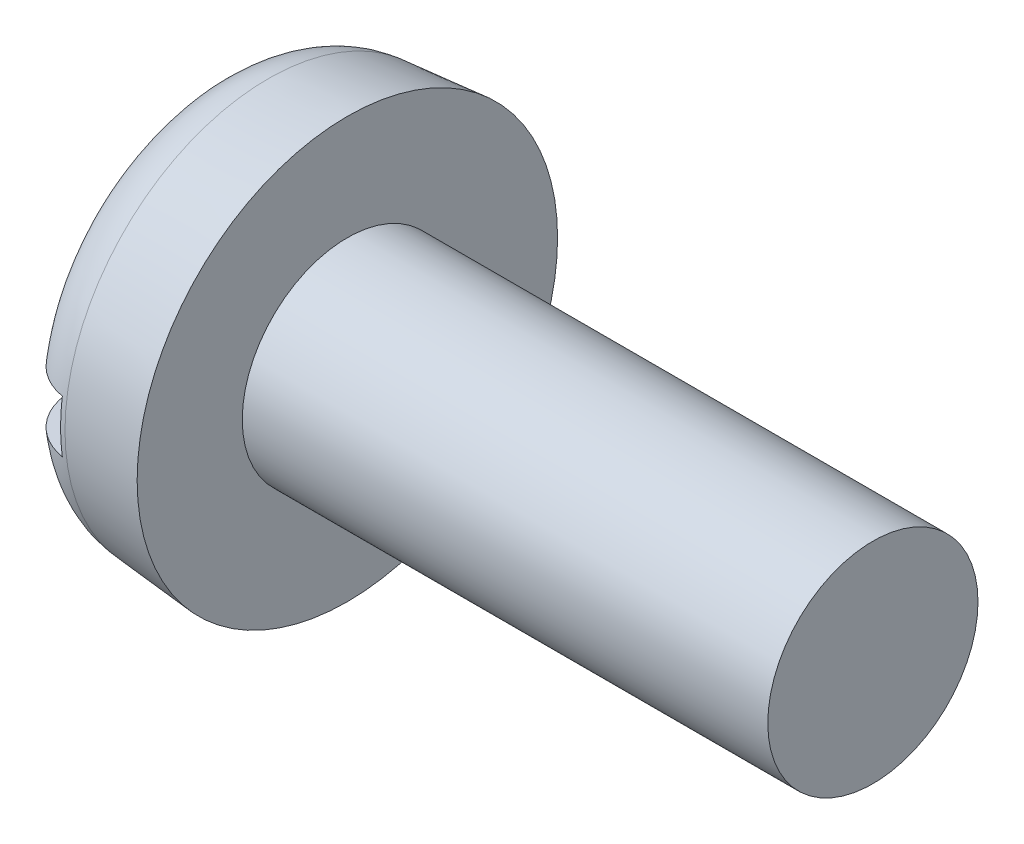
SolidWorks part; units mm, degrees
ref_plane "Plane1" through (0, 0, 0) normal (0, 0, 1) x (1, 0, 0)
ref_plane "Plane2" through (0, 0, 0) normal (0, 1, 0) x (1, 0, 0)
ref_plane "Plane3" through (0, 0, 0) normal (1, 0, 0) x (0, 0, -1)
sketch "BodySke" plane through (0, 0, 0) normal (0, 0, 1) x (1, 0, 0)
  line L0 (1.3, 1) -> (1.3, 2)
  line L1 (0, 0) -> (0, 1.8863)
  line L2 (-25.4, 0) -> (127, 0) construction
  line L3 (6.3, 0) -> (0, 0)
  line L4 (1.3, 1) -> (6.3, 1)
  line L5 (6.3, 1) -> (6.3, 0)
  line L6 (0, 1.8863) -> (1.3, 2)
  line L9 (1.7, 2.5875) -> (1.7, -6.9375) construction
  line L10 (1.3, 6.35) -> (1.3, -3.175) construction
  dimension "Head_ht" = 1.3
  dimension "Diameter" = 2
  dimension "Length" = 5
  dimension "Head_dia" = 4
  dimension "Advance" = 0.4
  dimension "Thread_nom" = 5
  dimension "Head_side_angle" = 5
revolve "Base-Revolve" add sketch "BodySke"
cosmetic thread "ThreadCosmetic"
fillet "Fillet1" [suppressed] radius 0.1
fillet "Fillet2" radius 0.6 1 edges at (0, 0, 1.8863)
sketch "Sketch2" plane through (0, 0, 0) normal (1, 0, 0) x (0, 0, -1)
  line L0 (2, -0.25) -> (-2, -0.25)
  line L1 (2, -0.25) -> (2, 0.25)
  line L2 (-2, 0.25) -> (2, 0.25)
  line L3 (-2, 0.25) -> (-2, -0.25)
  dimension "D1" = 4
  dimension "D2" = 2
  dimension "Slot_width" = 0.5
  dimension "D3" = 0.25
extrude "Slot" cut sketch "Sketch2" along normal blind 0.5
sketch "ThdSchSke" plane through (0, 0, 0) normal (0, 0, 1) x (1, 0, 0)
  line L0 (2.1, -0.774) -> (1.9418, -1)
  line L1 (2.1, -0.774) -> (2.2582, -1)
  line L2 (2.2582, -1) -> (2.2582, -1.25)
  line L3 (-3.175, 0) -> (5.1513, 0) construction
  line L5 (2.2582, -1.25) -> (1.9418, -1.25)
  line L6 (1.9418, -1.25) -> (1.9418, -1)
  dimension "Thread_minor" = 1.548
  dimension "Diameter" = 2
  dimension "Start" = 2.1
  dimension "SideAngle" = 55
  dimension "VeeAngle" = 70
  dimension "Overcut" = 2.5
revolve "ThreadSchematic" [suppressed] cut sketch "ThdSchSke" angle 360 about L3
pattern_linear "ThdSchPat" [suppressed]
equation "\"D1@Sketch2\" = \"Head_dia@BodySke\""
equation "\"D2@Sketch2\" = \"D1@Sketch2\" / 2"
equation "\"D3@Sketch2\" = \"Slot_width@Sketch2\" / 2"
equation "\"Thread_length@ThreadCosmetic\" = ((sgn( (\"Length@BodySke\" - \"Advance@BodySke\" * 2.0 ) - \"Thread_nom@BodySke\" )-1)*( (\"Length@BodySke\" - \"Advance@BodySke\"  * 2.0) - \"Thread_nom@BodySke\" ))/-2+ \"Thread_nom@BodySke\""
equation "\"Thread_minor@ThdSchSke\" = \"Thread_minor@ThreadCosmetic\""
equation "\"Diameter@ThdSchSke\" = \"Diameter@BodySke\""
equation "\"Overcut@ThdSchSke\" = \"Diameter@BodySke\" * 1.25"
equation "\"Start@ThdSchSke\" = \"Head_ht@BodySke\" + \"Length@BodySke\" - \"Thread_length@ThreadCosmetic\"  '---Non-countersunk---"
equation "\"Num_threads@ThdSchPat\" = int( \"Thread_length@ThreadCosmetic\" / \"Advance@BodySke\" + 0.999 )  + 1"
equation "\"Advance@ThdSchPat\" = \"Thread_length@ThreadCosmetic\" /  (\"Num_threads@ThdSchPat\" - 1) 'relax it"
